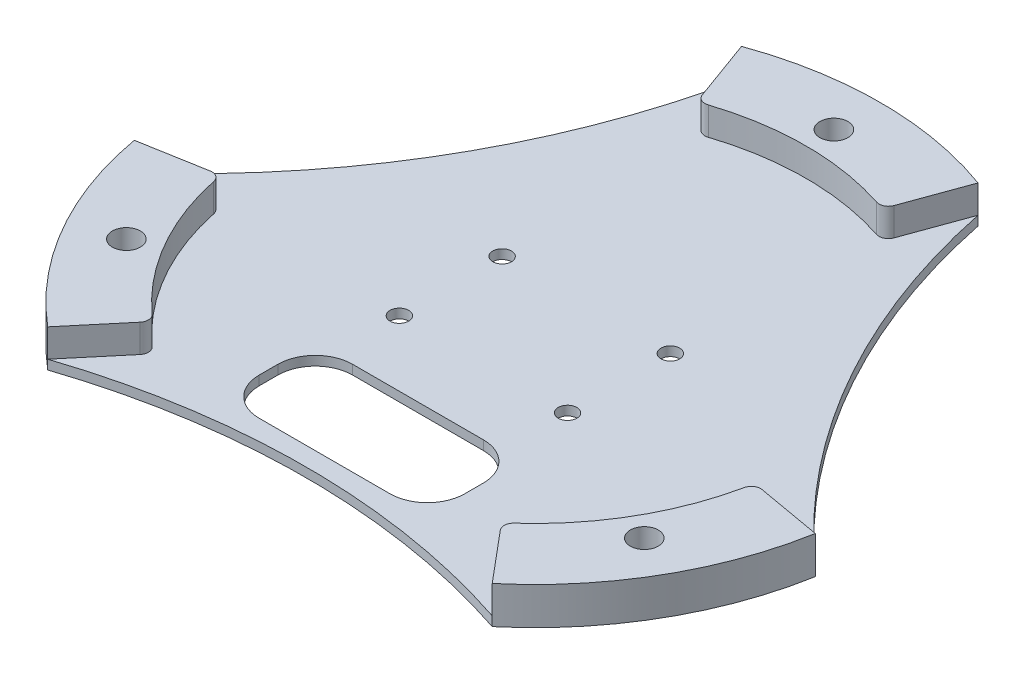
SolidWorks part; units mm, degrees
ref_plane "Front Plane" through (0, 0, 0) normal (0, 0, 1) x (1, 0, 0)
ref_plane "Top Plane" through (0, 0, 0) normal (0, 1, 0) x (1, 0, 0)
ref_plane "Right Plane" through (0, 0, 0) normal (1, 0, 0) x (0, 0, -1)
sketch "Sketch1" plane through (0, 0, 0) normal (0, 1, 0) x (1, 0, 0)
  circle A0 centre (0, 0) radius 37
  dimension "D1" = 74
extrude "Boss-Extrude1" add sketch "Sketch1" along normal blind 1
sketch "Sketch2" plane through (0, 1, 0) normal (0, 1, 0) x (1, 0, 0)
  line L0 (-12.6547, 34.7686) -> (0, 0) construction
  line L1 (0, 0) -> (12.6547, 34.7686) construction
  line L2 (0, -1000) -> (0, 49000) construction
  line L3 (-12.6547, 34.7686) -> (-9.9186, 27.2511)
  line L4 (9.9186, 27.2511) -> (12.6547, 34.7686)
  arc A0 (12.6547, 34.7686) -> (-12.6547, 34.7686) centre (0, 0) ccw
  circle A1 centre (0, 0) radius 37 construction
  arc A2 (9.9186, 27.2511) -> (-9.9186, 27.2511) centre (0, 0) ccw
  circle A3 centre (0, 32) radius 1.5
  dimension "D1" = 8
  dimension "D5" = 3
  dimension "D2" = 20
  dimension "D3" = 20
  dimension "D4" = 32
extrude "Boss-Extrude2" add sketch "Sketch2" along normal blind 3
sketch "Sketch16" plane through (0, 4, 0) normal (0, 1, 0) x (1, 0, 0)
  circle A0 centre (0, 32) radius 1.5
  circle A1 centre (0, 32) radius 1.5 construction
extrude "Cut-Extrude9" cut sketch "Sketch16" against normal through all
pattern_circular "CirPattern1" count 3 over 360 about axis through (0, 0, 0) along (0, 1, 0) of "Boss-Extrude2", "Cut-Extrude9"
sketch "Sketch5" plane through (0, 1, 0) normal (0, 1, 0) x (1, 0, 0)
  circle A1 centre (86.6025, 50) radius 75.5001
  dimension "D1" = 100
extrude "Cut-Extrude3" cut sketch "Sketch5" against normal through all
pattern_circular "CirPattern2" count 3 over 360 about axis through (0, 0, 0) along (0, 1, 0) of "Cut-Extrude3"
fillet "Fillet2" radius 1 6 edges at (28.5594, 2.5, 5.0358) (9.9186, 2.5, -27.2511) (-9.9186, 2.5, -27.2511) (18.6408, 2.5, 22.2153) (-28.5594, 2.5, 5.0358) (-18.6408, 2.5, 22.2153)
sketch "Sketch18" plane through (0, 1, 0) normal (0, 1, 0) x (1, 0, 0)
  line L0 (-1000, 0) -> (49000, 0) construction
  line L1 (-9, -5.5) -> (9, -5.5) construction
  line L2 (-9, -5.5) -> (-9, 5.5) construction
  line L3 (-9, 5.5) -> (9, 5.5) construction
  line L4 (9, -5.5) -> (9, 5.5) construction
  line L5 (-9, -5.5) -> (9, 5.5) construction
  line L6 (-9, 5.5) -> (9, -5.5) construction
  circle A0 centre (9, 5.5) radius 1
  circle A1 centre (-9, 5.5) radius 1
  circle A2 centre (9, -5.5) radius 1
  circle A3 centre (-9, -5.5) radius 1
  point P0 (0, 0)
  dimension "D1" = 2
  dimension "D2" = 11
  dimension "D3" = 18
extrude "Cut-Extrude10" cut sketch "Sketch18" against normal through all
sketch "Sketch20" plane through (0, 1, 0) normal (0, 1, 0) x (1, 0, 0)
  line L1 (11, -22.5) -> (-11, -22.5) construction
  line L2 (11, -22.5) -> (11, 7.5) construction
  line L3 (11, 7.5) -> (-11, 7.5) construction
  line L4 (-11, -22.5) -> (-11, 7.5) construction
  line L5 (11, -22.5) -> (-11, 7.5) construction
  line L6 (11, 7.5) -> (-11, -22.5) construction
  line L7 (-11, -22.5) -> (11, -22.5)
  line L8 (-11, -22.5) -> (-11, -12.5)
  line L9 (-11, -12.5) -> (11, -12.5)
  line L10 (11, -22.5) -> (11, -12.5)
  circle A0 centre (9, 5.5) radius 1 construction
  point P0 (0, -7.5)
  dimension "D3" = 2
  dimension "D1" = 22
  dimension "D2" = 30
  dimension "D4" = 10
extrude "Cut-Extrude12" cut sketch "Sketch20" against normal through all
fillet "Fillet3" radius 4 4 edges at (11, 0.5, 12.5) (-11, 0.5, 12.5) (11, 0.5, 22.5) (-11, 0.5, 22.5)
